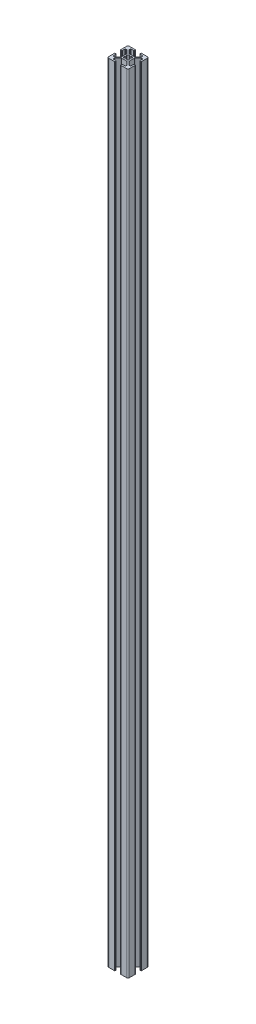
SolidWorks part; units mm, degrees
material "6061 Alloy"
ref_plane "Front Plane" through (0, 0, 0) normal (0, 0, 1) x (1, 0, 0)
ref_plane "Top Plane" through (0, 0, 0) normal (0, 1, 0) x (1, 0, 0)
ref_plane "Right Plane" through (0, 0, 0) normal (1, 0, 0) x (0, 0, -1)
sketch "Sketch1" plane through (0, 0, 0) normal (0, 0, 1) x (1, 0, 0)
  line L0 (0, 380) -> (0, -380)
  point P4 (0, 0)
  dimension "D1" = 760
other " C:\\PROGRAM FILES\\SOLIDWORKS CORP\\SOLIDWORKS\\LANG\\ENGLISH\\WELDMENT PROFILES\\BOSCH PROFILES\\20_SERIES\\20-2020-BLACK-FB - IS MISSING(1)"
ref_plane "Plane1" through (0, 380, 0) normal (0, -1, 0) x (1, 0, 0)
sketch "Sketch11" plane through (0, 380, 0) normal (0, -1, 0) x (1, 0, 0)
  line L0 (9.0094, 2.6289) -> (9.492, 2.6289)
  line L1 (8.5014, 5.4864) -> (8.5014, 3.1369)
  line L2 (10, 8.5014) -> (10, 3.1369)
  line L3 (7.2645, 5.9944) -> (7.9934, 5.9944)
  line L4 (3.1369, 10) -> (8.5014, 10)
  line L5 (3.8074, 2.7477) -> (6.9053, 5.8456)
  line L6 (2.6289, 9.0094) -> (2.6289, 9.492)
  line L7 (3.6586, -2.3885) -> (3.6586, 2.3885)
  line L8 (3.1369, 8.5014) -> (5.4864, 8.5014)
  line L9 (6.9053, -5.8456) -> (3.8074, -2.7477)
  line L10 (5.9944, 7.9934) -> (5.9944, 7.2645)
  line L11 (7.9934, -5.9944) -> (7.2645, -5.9944)
  line L12 (5.8456, 6.9053) -> (2.7477, 3.8074)
  line L13 (8.5014, -3.1369) -> (8.5014, -5.4864)
  line L14 (2.3885, 3.6586) -> (-2.3885, 3.6586)
  line L15 (9.0094, -2.6289) -> (9.492, -2.6289)
  line L16 (-2.7477, 3.8074) -> (-5.8456, 6.9053)
  line L17 (10, -3.1369) -> (10, -8.5014)
  line L18 (-5.9944, 7.2645) -> (-5.9944, 7.9934)
  line L19 (8.5014, -10) -> (3.1369, -10)
  line L20 (-5.4864, 8.5014) -> (-3.1369, 8.5014)
  line L21 (2.6289, -9.0094) -> (2.6289, -9.492)
  line L22 (-2.6289, 9.0094) -> (-2.6289, 9.492)
  line L23 (5.4864, -8.5014) -> (3.1369, -8.5014)
  line L24 (-8.5014, 10) -> (-3.1369, 10)
  line L25 (5.9944, -7.2645) -> (5.9944, -7.9934)
  line L26 (-10, 3.1369) -> (-10, 8.5014)
  line L27 (2.7477, -3.8074) -> (5.8456, -6.9053)
  line L28 (-9.0094, 2.6289) -> (-9.492, 2.6289)
  line L29 (-2.3885, -3.6586) -> (2.3885, -3.6586)
  line L30 (-8.5014, 3.1369) -> (-8.5014, 5.4864)
  line L31 (-5.8456, -6.9053) -> (-2.7477, -3.8074)
  line L32 (-7.9934, 5.9944) -> (-7.2645, 5.9944)
  line L33 (-5.9944, -7.9934) -> (-5.9944, -7.2645)
  line L34 (-6.9053, 5.8456) -> (-3.8074, 2.7477)
  line L35 (-3.1369, -8.5014) -> (-5.4864, -8.5014)
  line L36 (-3.6586, 2.3885) -> (-3.6586, -2.3885)
  line L37 (-2.6289, -9.0094) -> (-2.6289, -9.492)
  line L38 (-3.8074, -2.7477) -> (-6.9053, -5.8456)
  line L39 (-3.1369, -10) -> (-8.5014, -10)
  line L40 (-7.2645, -5.9944) -> (-7.9934, -5.9944)
  line L41 (-10, -8.5014) -> (-10, -3.1369)
  line L42 (-8.5014, -5.4864) -> (-8.5014, -3.1369)
  line L43 (-9.0094, -2.6289) -> (-9.492, -2.6289)
  line L44 (-2.2966, 2.1217) -> (-2.1217, 2.2966)
  line L45 (2.1217, 2.2966) -> (2.2966, 2.1217)
  line L46 (-2.1217, -2.2966) -> (-2.2966, -2.1217)
  line L47 (2.2966, -2.1217) -> (2.1217, -2.2966)
  arc A0 (8.5014, 3.1369) -> (9.0094, 2.6289) centre (9.0094, 3.1369) ccw
  arc A1 (9.492, 2.6289) -> (10, 3.1369) centre (9.492, 3.1369) ccw
  arc A2 (8.5014, 5.4864) -> (7.9934, 5.9944) centre (7.9934, 5.4864) ccw
  arc A3 (10, 8.5014) -> (8.5014, 10) centre (8.5014, 8.5014) ccw
  arc A4 (7.2645, 5.9944) -> (6.9053, 5.8456) centre (7.2645, 5.4864) ccw
  arc A5 (3.1369, 10) -> (2.6289, 9.492) centre (3.1369, 9.492) ccw
  arc A6 (3.8074, 2.7477) -> (3.6586, 2.3885) centre (4.1666, 2.3885) ccw
  arc A7 (2.6289, 9.0094) -> (3.1369, 8.5014) centre (3.1369, 9.0094) ccw
  arc A8 (3.6586, -2.3885) -> (3.8074, -2.7477) centre (4.1666, -2.3885) ccw
  arc A9 (5.9944, 7.9934) -> (5.4864, 8.5014) centre (5.4864, 7.9934) ccw
  arc A10 (6.9053, -5.8456) -> (7.2645, -5.9944) centre (7.2645, -5.4864) ccw
  arc A11 (5.8456, 6.9053) -> (5.9944, 7.2645) centre (5.4864, 7.2645) ccw
  arc A12 (7.9934, -5.9944) -> (8.5014, -5.4864) centre (7.9934, -5.4864) ccw
  arc A13 (2.3885, 3.6586) -> (2.7477, 3.8074) centre (2.3885, 4.1666) ccw
  arc A14 (9.0094, -2.6289) -> (8.5014, -3.1369) centre (9.0094, -3.1369) ccw
  arc A15 (-2.7477, 3.8074) -> (-2.3885, 3.6586) centre (-2.3885, 4.1666) ccw
  arc A16 (10, -3.1369) -> (9.492, -2.6289) centre (9.492, -3.1369) ccw
  arc A17 (-5.9944, 7.2645) -> (-5.8456, 6.9053) centre (-5.4864, 7.2645) ccw
  arc A18 (8.5014, -10) -> (10, -8.5014) centre (8.5014, -8.5014) ccw
  arc A19 (-5.4864, 8.5014) -> (-5.9944, 7.9934) centre (-5.4864, 7.9934) ccw
  arc A20 (2.6289, -9.492) -> (3.1369, -10) centre (3.1369, -9.492) ccw
  arc A21 (-3.1369, 8.5014) -> (-2.6289, 9.0094) centre (-3.1369, 9.0094) ccw
  arc A22 (3.1369, -8.5014) -> (2.6289, -9.0094) centre (3.1369, -9.0094) ccw
  arc A23 (-2.6289, 9.492) -> (-3.1369, 10) centre (-3.1369, 9.492) ccw
  arc A24 (5.4864, -8.5014) -> (5.9944, -7.9934) centre (5.4864, -7.9934) ccw
  arc A25 (-8.5014, 10) -> (-10, 8.5014) centre (-8.5014, 8.5014) ccw
  arc A26 (5.9944, -7.2645) -> (5.8456, -6.9053) centre (5.4864, -7.2645) ccw
  arc A27 (-10, 3.1369) -> (-9.492, 2.6289) centre (-9.492, 3.1369) ccw
  arc A28 (2.7477, -3.8074) -> (2.3885, -3.6586) centre (2.3885, -4.1666) ccw
  arc A29 (-9.0094, 2.6289) -> (-8.5014, 3.1369) centre (-9.0094, 3.1369) ccw
  arc A30 (-2.3885, -3.6586) -> (-2.7477, -3.8074) centre (-2.3885, -4.1666) ccw
  arc A31 (-7.9934, 5.9944) -> (-8.5014, 5.4864) centre (-7.9934, 5.4864) ccw
  arc A32 (-5.8456, -6.9053) -> (-5.9944, -7.2645) centre (-5.4864, -7.2645) ccw
  arc A33 (-6.9053, 5.8456) -> (-7.2645, 5.9944) centre (-7.2645, 5.4864) ccw
  arc A34 (-5.9944, -7.9934) -> (-5.4864, -8.5014) centre (-5.4864, -7.9934) ccw
  arc A35 (-3.6586, 2.3885) -> (-3.8074, 2.7477) centre (-4.1666, 2.3885) ccw
  arc A36 (-2.6289, -9.0094) -> (-3.1369, -8.5014) centre (-3.1369, -9.0094) ccw
  arc A37 (-3.8074, -2.7477) -> (-3.6586, -2.3885) centre (-4.1666, -2.3885) ccw
  arc A38 (-3.1369, -10) -> (-2.6289, -9.492) centre (-3.1369, -9.492) ccw
  arc A39 (-7.2645, -5.9944) -> (-6.9053, -5.8456) centre (-7.2645, -5.4864) ccw
  arc A40 (-10, -8.5014) -> (-8.5014, -10) centre (-8.5014, -8.5014) ccw
  arc A41 (-8.5014, -5.4864) -> (-7.9934, -5.9944) centre (-7.9934, -5.4864) ccw
  arc A42 (-9.492, -2.6289) -> (-10, -3.1369) centre (-9.492, -3.1369) ccw
  arc A43 (-8.5014, -3.1369) -> (-9.0094, -2.6289) centre (-9.0094, -3.1369) ccw
  arc A44 (-0.8806, 2.1293) -> (-0.5885, 2.0112) centre (-0.6599, 2.2549) ccw
  arc A45 (0.5885, 2.0112) -> (-0.5885, 2.0112) centre (0, 0) ccw
  arc A46 (-0.8806, 2.1293) -> (-2.1217, 2.2966) centre (-1.565, 1.7398) ccw
  arc A47 (0.5885, 2.0112) -> (0.8806, 2.1293) centre (0.6599, 2.2549) ccw
  arc A48 (2.1217, 2.2966) -> (0.8806, 2.1293) centre (1.565, 1.7398) ccw
  arc A49 (-2.2966, 2.1217) -> (-2.1293, 0.8806) centre (-1.7398, 1.565) ccw
  arc A50 (-2.0112, 0.5885) -> (-2.1293, 0.8806) centre (-2.2549, 0.6599) ccw
  arc A51 (2.1293, 0.8806) -> (2.2966, 2.1217) centre (1.7398, 1.565) ccw
  arc A52 (-2.0112, 0.5885) -> (-2.0112, -0.5885) centre (0, 0) ccw
  arc A53 (2.1293, 0.8806) -> (2.0112, 0.5885) centre (2.2549, 0.6599) ccw
  arc A54 (-2.1293, -0.8806) -> (-2.0112, -0.5885) centre (-2.2549, -0.6599) ccw
  arc A55 (2.0112, -0.5885) -> (2.0112, 0.5885) centre (0, 0) ccw
  arc A56 (-2.1293, -0.8806) -> (-2.2966, -2.1217) centre (-1.7398, -1.565) ccw
  arc A57 (2.0112, -0.5885) -> (2.1293, -0.8806) centre (2.2549, -0.6599) ccw
  arc A58 (2.2966, -2.1217) -> (2.1293, -0.8806) centre (1.7398, -1.565) ccw
  arc A59 (-2.1217, -2.2966) -> (-0.8806, -2.1293) centre (-1.565, -1.7398) ccw
  arc A60 (-0.5885, -2.0112) -> (-0.8806, -2.1293) centre (-0.6599, -2.2549) ccw
  arc A61 (0.8806, -2.1293) -> (2.1217, -2.2966) centre (1.565, -1.7398) ccw
  arc A62 (-0.5885, -2.0112) -> (0.5885, -2.0112) centre (0, 0) ccw
  arc A63 (0.8806, -2.1293) -> (0.5885, -2.0112) centre (0.6599, -2.2549) ccw
  point P0 (0, 0)
